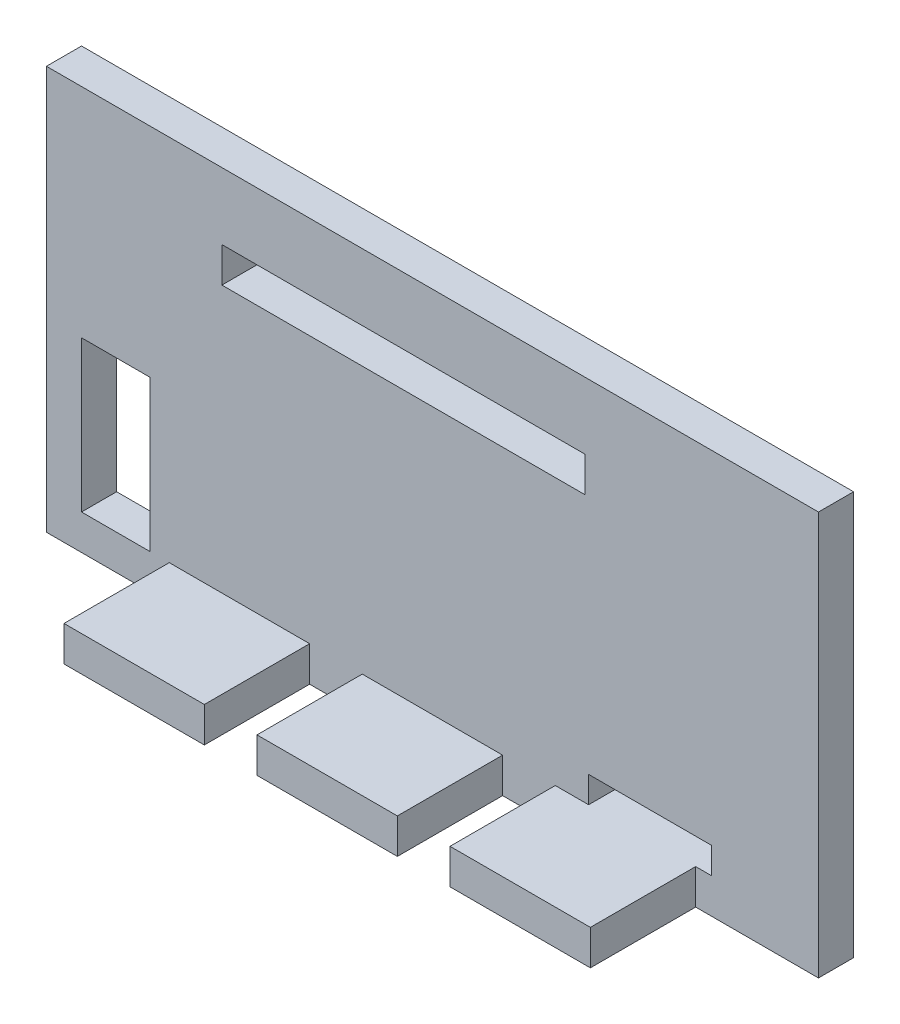
SolidWorks part; units mm, degrees
ref_plane "Front Plane" through (0, 0, 0) normal (0, 0, 1) x (1, 0, 0)
ref_plane "Top Plane" through (0, 0, 0) normal (0, 1, 0) x (1, 0, 0)
ref_plane "Right Plane" through (0, 0, 0) normal (1, 0, 0) x (0, 0, -1)
sketch "Sketch1" plane through (0, 0, 0) normal (0, 0, 1) x (1, 0, 0)
  line L1 (-22, 11.5) -> (22, 11.5)
  line L2 (-22, 11.5) -> (-22, -11.5)
  line L3 (-22, -11.5) -> (22, -11.5)
  line L4 (22, 11.5) -> (22, -11.5)
  line L5 (-22, 11.5) -> (22, -11.5) construction
  line L6 (-22, -11.5) -> (22, 11.5) construction
  point P0 (0, 0)
extrude "Boss-Extrude1" add sketch "Sketch1" along normal blind 2
sketch "Sketch2" plane through (0, 0, 2) normal (0, 0, 1) x (1, 0, 0)
  line L0 (-22, -11.5) -> (-22, -9.5) construction
  line L1 (-22, 11.5) -> (-22, -11.5) construction
  line L2 (-22, -9.5) -> (-20, -9.5) construction
  line L3 (-16.1, -9.5) -> (8.9, -9.5) construction
  line L4 (-20, -9.5) -> (-16.1, -9.5)
  line L5 (-20, -9.5) -> (-20, -0.9)
  line L6 (-20, -0.9) -> (-16.1, -0.9)
  line L7 (-16.1, -9.5) -> (-16.1, -0.9)
  line L8 (-22, 11.5) -> (-12, 11.5) construction
  line L9 (8.9, -9.5) -> (15.9, -9.5)
  line L10 (8.9, -9.5) -> (8.9, -8)
  line L11 (8.9, -8) -> (15.9, -8)
  line L12 (15.9, -9.5) -> (15.9, -8)
  line L13 (22, 11.5) -> (-22, 11.5) construction
  line L14 (-12, 11.5) -> (-12, 5.7) construction
  line L16 (-12, 5.7) -> (8.7, 5.7)
  line L17 (-12, 5.7) -> (-12, 7.7)
  line L18 (-12, 7.7) -> (8.7, 7.7)
  line L19 (8.7, 5.7) -> (8.7, 7.7)
extrude "Cut-Extrude1" cut sketch "Sketch2" against normal blind 2
sketch "Sketch4" plane through (0, 0, 2) normal (0, 0, 1) x (1, 0, 0)
  line L0 (-22, -11.5) -> (-15, -11.5) construction
  line L1 (-22, -11.5) -> (22, -11.5) construction
  line L2 (-7, -11.5) -> (-4, -11.5) construction
  line L3 (-15, -11.5) -> (-7, -11.5)
  line L4 (-15, -11.5) -> (-15, -9.5)
  line L5 (-15, -9.5) -> (-7, -9.5)
  line L6 (-7, -11.5) -> (-7, -9.5)
  line L7 (4, -11.5) -> (7, -11.5) construction
  line L8 (-4, -11.5) -> (4, -11.5)
  line L9 (-4, -11.5) -> (-4, -9.5)
  line L10 (-4, -9.5) -> (4, -9.5)
  line L11 (4, -11.5) -> (4, -9.5)
  line L12 (8.9, -9.5) -> (15.9, -9.5) construction
  line L13 (7, -11.5) -> (15, -11.5)
  line L14 (7, -11.5) -> (7, -9.5)
  line L15 (7, -9.5) -> (15, -9.5)
  line L16 (15, -11.5) -> (15, -9.5)
extrude "Boss-Extrude2" add sketch "Sketch4" along normal blind 6
